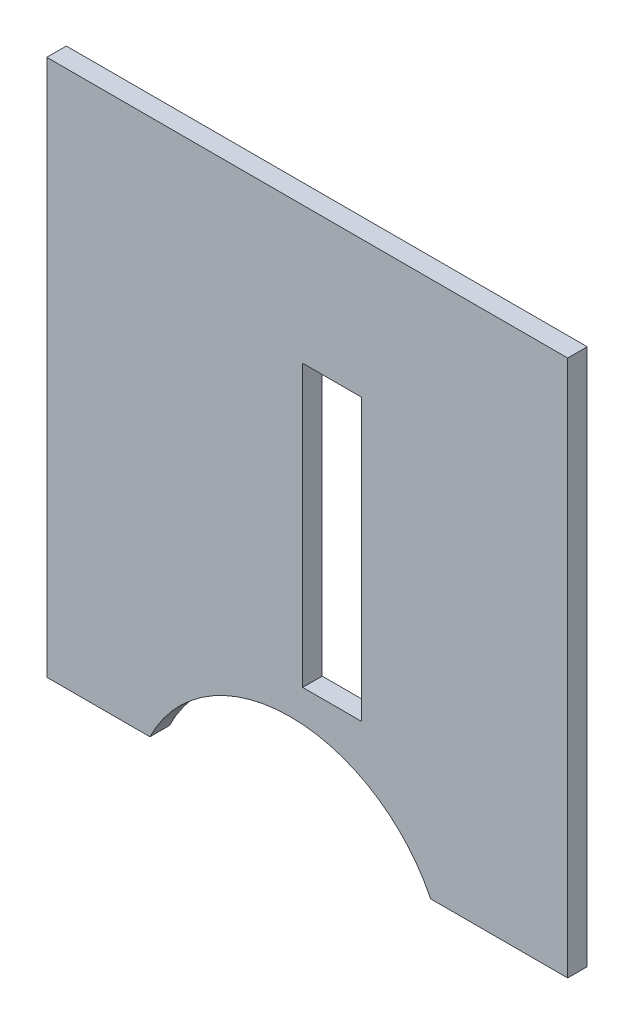
SolidWorks part; units mm, degrees
ref_plane "Front Plane" through (0, 0, 0) normal (0, 0, 1) x (1, 0, 0)
ref_plane "Top Plane" through (0, 0, 0) normal (0, 1, 0) x (1, 0, 0)
ref_plane "Right Plane" through (0, 0, 0) normal (1, 0, 0) x (0, 0, -1)
sketch "Sketch1" plane through (0, 0, 0) normal (0, 0, 1) x (1, 0, 0)
  line L0 (0, -82.457) -> (15.8432, -82.457)
  line L1 (0, 0) -> (80, 0)
  line L2 (0, 0) -> (0, -82.457)
  line L3 (0, -82.457) -> (80, -82.457) construction
  line L4 (80, 0) -> (80, -82.457)
  line L5 (39.3, -21.0432) -> (48.3, -21.0432)
  line L6 (39.3, -21.0432) -> (39.3, -64.1568)
  line L7 (39.3, -64.1568) -> (48.3, -64.1568)
  line L8 (48.3, -21.0432) -> (48.3, -64.1568)
  line L9 (58.9568, -82.457) -> (80, -82.457)
  circle A0 centre (37.4, -93.007) radius 21 construction
  arc A1 (58.9568, -82.457) -> (15.8432, -82.457) centre (37.4, -93.007) ccw
  circle A2 centre (37.4, -93.007) radius 21 construction
  dimension "D1" = 3
sketch "Sketch2" plane through (0, 0, 0) normal (0, 1, 0) x (1, 0, 0)
  line L1 (80, 0) -> (0, 0)
  line L2 (80, 0) -> (80, 3)
  line L3 (80, 3) -> (0, 3)
  line L4 (0, 0) -> (0, 3)
extrude "Boss-Extrude1" add sketch "Sketch1" against normal up to vertex (3 mm away) up to point (0, 0, -3)
